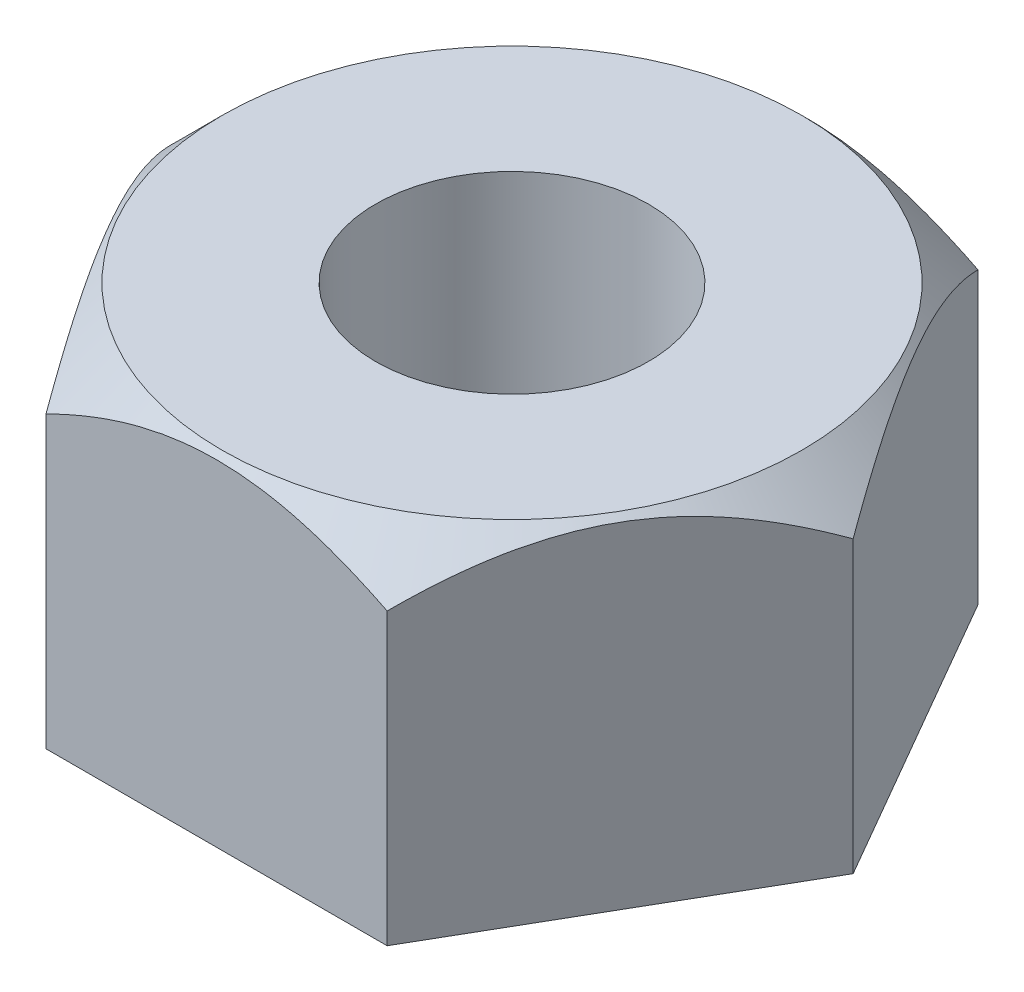
SolidWorks part; units mm, degrees
ref_plane "Front Plane" through (0, 0, 0) normal (0, 0, 1) x (1, 0, 0)
ref_plane "Top Plane" through (0, 0, 0) normal (0, 1, 0) x (1, 0, 0)
ref_plane "Right Plane" through (0, 0, 0) normal (1, 0, 0) x (0, 0, -1)
sketch "Sketch1" plane through (0, 0, 0) normal (0, 1, 0) x (1, 0, 0)
  line L0 (0, 8.1278) -> (0, -7.1586) construction
  line L1 (5, 0) -> (2.5, 4.3301)
  line L2 (2.5, 4.3301) -> (-2.5, 4.3301)
  line L3 (-2.5, 4.3301) -> (-5, 0)
  line L4 (-5, 0) -> (-2.5, -4.3301)
  line L5 (-2.5, -4.3301) -> (2.5, -4.3301)
  line L6 (2.5, -4.3301) -> (5, 0)
  circle A0 centre (0, 0) radius 4.3301 construction
  circle A1 centre (0, 0) radius 2
  dimension "D2" = 4
  dimension "D1" = 10
extrude "Boss-Extrude1" add sketch "Sketch1" along normal blind 5
sketch "Sketch2" plane through (0, 5, 0) normal (0, 1, 0) x (1, 0, 0)
  circle A0 centre (0, 0) radius 4.25
  dimension "D1" = 8.5
extrude "Cut-Extrude1" cut sketch "Sketch2" against normal blind 5 draft 45 flip side to cut
